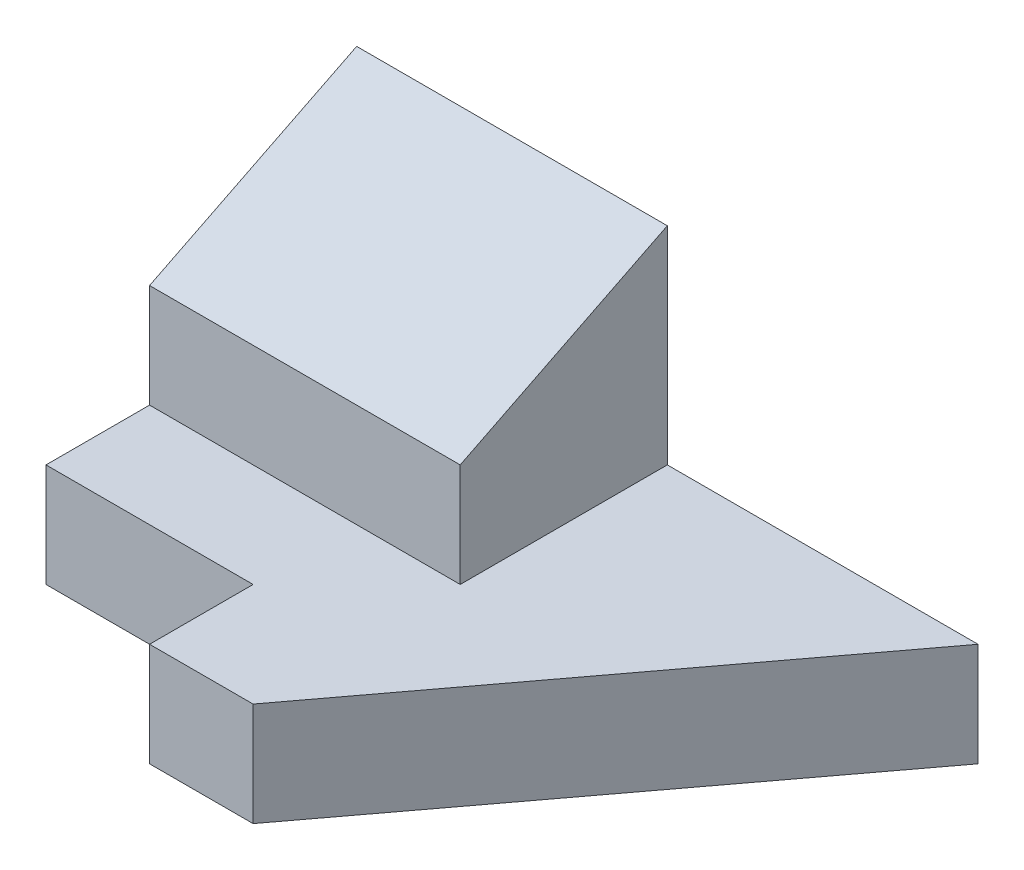
SolidWorks part; units mm, degrees
material "Copper"
ref_plane "Front Plane" through (0, 0, 0) normal (0, 0, 1) x (1, 0, 0)
ref_plane "Top Plane" through (0, 0, 0) normal (0, 1, 0) x (1, 0, 0)
ref_plane "Right Plane" through (0, 0, 0) normal (1, 0, 0) x (0, 0, -1)
sketch "Sketch1" plane through (0, 0, 0) normal (0, 1, 0) x (1, 0, 0)
  line L0 (0, 0) -> (20, 0)
  line L1 (20, 0) -> (20, -10)
  line L2 (20, -10) -> (30, -10)
  line L3 (0, 0) -> (0, 30)
  line L4 (0, 30) -> (60, 30)
  line L5 (30, -10) -> (60, 30)
  dimension "D1" = 50
  dimension "D2" = 60
extrude "Boss-Extrude1" add sketch "Sketch1" along normal blind 10
sketch "Sketch5" plane through (0, 0, 0) normal (-1, 0, 0) x (0, 0, 1)
  line L1 (-30, 10) -> (-10, 10)
  line L2 (-30, 10) -> (-30, 20)
  line L3 (-30, 20) -> (-10, 20)
  line L4 (-10, 10) -> (-10, 20)
extrude "Boss-Extrude4" add sketch "Sketch5" against normal blind 30
sketch "Sketch7" plane through (0, 0, 0) normal (1, 0, 0) x (0, 0, -1)
  line L0 (30, 20) -> (30, 30)
  line L1 (10, 20) -> (30, 20) construction
  line L2 (30, 30) -> (10, 20)
  line L9 (0, 0) -> (30, 0)
  line L10 (0, 10) -> (0, 0)
  line L11 (10, 10) -> (0, 10)
  line L12 (10, 20) -> (10, 10)
  line L13 (30, 20) -> (10, 20)
  line L14 (30, 0) -> (30, 20)
  line L19 (30, 20) -> (10, 20)
  dimension "D1" = 0
extrude "Boss-Extrude5" add sketch "Sketch7" along normal blind 30 contours L0 L2 L19
